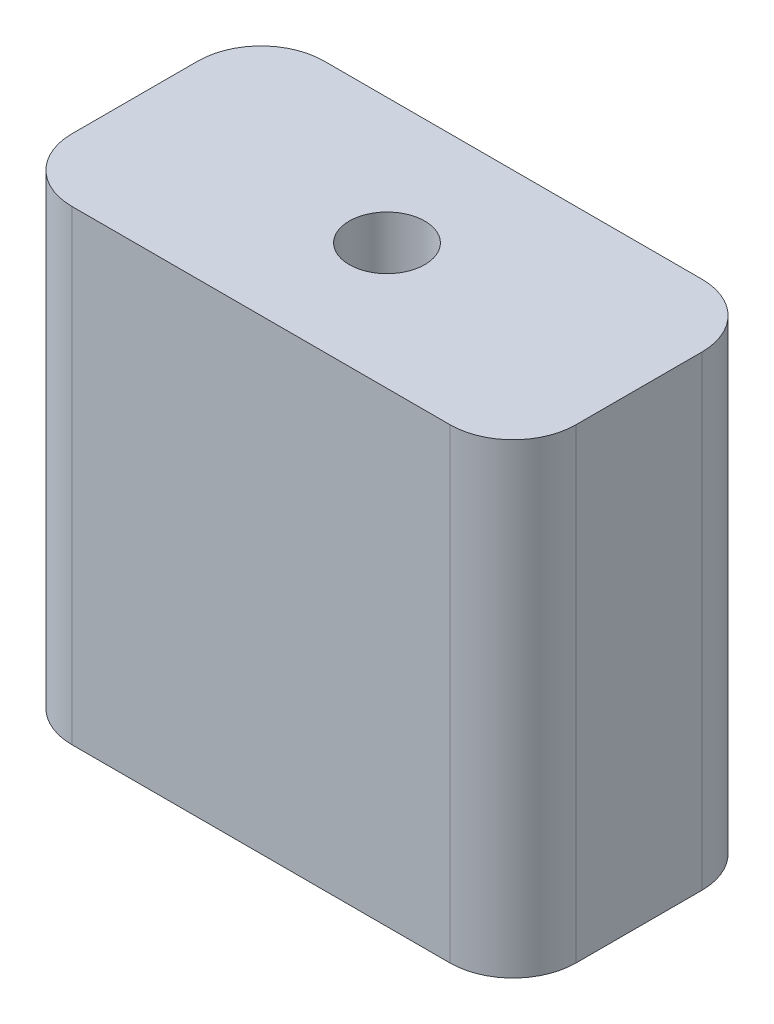
SolidWorks part; units mm, degrees
ref_plane "Front Plane" through (0, 0, 0) normal (0, 0, 1) x (1, 0, 0)
ref_plane "Top Plane" through (0, 0, 0) normal (0, 1, 0) x (1, 0, 0)
ref_plane "Right Plane" through (0, 0, 0) normal (1, 0, 0) x (0, 0, -1)
sketch "Sketch1" plane through (0, 0, 0) normal (0, 1, 0) x (1, 0, 0)
  line L1 (-20, -10) -> (20, -10)
  line L2 (-20, -10) -> (-20, 10)
  line L3 (-20, 10) -> (20, 10)
  line L4 (20, -10) -> (20, 10)
  line L5 (-20, -10) -> (20, 10) construction
  line L6 (-20, 10) -> (20, -10) construction
  point P0 (0, 0)
  dimension "D1" = 40
  dimension "D2" = 20
extrude "Boss-Extrude1" add sketch "Sketch1" along normal blind 37
fillet "Fillet1" radius 5 4 edges at (-20, 18.5, -10) (-20, 18.5, 10) (20, 18.5, -10) (20, 18.5, 10)
sketch "Sketch2" plane through (0, 37, 0) normal (0, 1, 0) x (1, 0, 0)
  circle A0 centre (0, 0) radius 3
  dimension "D1" = 6
extrude "Cut-Extrude1" cut sketch "Sketch2" against normal blind 5
